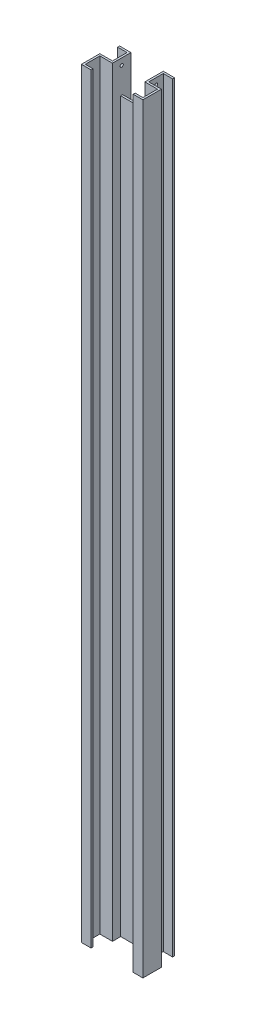
SolidWorks part; units mm, degrees
ref_plane "Front Plane" through (0, 0, 0) normal (0, 0, 1) x (1, 0, 0)
ref_plane "Top Plane" through (0, 0, 0) normal (0, 1, 0) x (1, 0, 0)
ref_plane "Right Plane" through (0, 0, 0) normal (1, 0, 0) x (0, 0, -1)
ref_plane "Plane1" through (0, 0, -76.5) normal (0, 0, -1) x (-1, 0, 0)
sketch "Sketch1" plane through (0, 0, -76.5) normal (0, 0, -1) x (-1, 0, 0)
  line L0 (-95, 0) -> (-50, 0)
  line L1 (-50, 0) -> (-50, 2350)
  line L2 (-50, 2350) -> (-95, 2350)
  line L3 (-95, 2350) -> (-95, 0)
extrude "Boss-Extrude1" add sketch "Sketch1" against normal blind 31.5
sketch "Sketch2" plane through (50, 0, 0) normal (-1, 0, 0) x (0, 0, 1)
  line L0 (-70.5, 0) -> (-76.5, 0)
  line L1 (-76.5, 0) -> (-76.5, 2350)
  line L2 (-76.5, 2350) -> (-70.5, 2350)
  line L3 (-70.5, 2350) -> (-70.5, 0)
extrude "Boss-Extrude2" add sketch "Sketch2" along normal blind 145
sketch "Sketch3" plane through (0, 0, -70.5) normal (0, 0, 1) x (1, 0, 0)
  line L0 (-50, 0) -> (-95, 0)
  line L1 (-95, 0) -> (-95, 2350)
  line L2 (-95, 2350) -> (-50, 2350)
  line L3 (-50, 2350) -> (-50, 0)
extrude "Boss-Extrude3" add sketch "Sketch3" along normal blind 76.5
sketch "Sketch4" plane through (0, 0, -45) normal (0, 0, 1) x (1, 0, 0)
  line L0 (89, 2350) -> (95, 2350)
  line L1 (95, 2350) -> (95, 0)
  line L2 (95, 0) -> (89, 0)
  line L3 (89, 0) -> (89, 2350)
extrude "Boss-Extrude4" add sketch "Sketch4" along normal blind 51
sketch "Sketch5" plane through (89, 0, 0) normal (-1, 0, 0) x (0, 0, 1)
  line L0 (6, 0) -> (0, 0)
  line L1 (0, 0) -> (0, 2350)
  line L2 (0, 2350) -> (6, 2350)
  line L3 (6, 2350) -> (6, 0)
extrude "Boss-Extrude5" add sketch "Sketch5" along normal blind 24
sketch "Sketch6" plane through (0, 0, 6) normal (0, 0, 1) x (1, 0, 0)
  line L0 (-65, 2350) -> (-65, 0)
  line L1 (-65, 0) -> (-50, 0)
  line L2 (-50, 0) -> (-50, 2350)
  line L3 (-50, 2350) -> (-65, 2350)
extrude "Cut-Extrude1" cut sketch "Sketch6" against normal blind 6
sketch "Sketch7" plane through (0, 0, 0) normal (0, 0, 1) x (1, 0, 0)
  line L0 (-89, 0) -> (-50, 0)
  line L1 (-50, 0) -> (-50, 2350)
  line L2 (-50, 2350) -> (-89, 2350)
  line L3 (-89, 2350) -> (-89, 0)
extrude "Cut-Extrude2" cut sketch "Sketch7" against normal blind 45
sketch "Sketch8" plane through (0, 2350, 0) normal (0, 1, 0) x (-1, 0, 0)
  line L0 (50, -76.5) -> (50, -70.5)
  line L1 (50, -70.5) -> (-50, -70.5)
  line L2 (-50, -70.5) -> (-50, -76.5)
  line L3 (-50, -76.5) -> (50, -76.5)
extrude "Cut-Extrude3" cut sketch "Sketch8" against normal blind 100
sketch "Sketch9" plane through (0, 0, -76.5) normal (0, 0, -1) x (-1, 0, 0)
  line L0 (-95, 2350) -> (-50, 2350)
  line L1 (-50, 2350) -> (-50, 0)
  line L2 (-50, 0) -> (-95, 0)
  line L3 (-95, 0) -> (-95, 2350)
extrude "Boss-Extrude6" add sketch "Sketch9" along normal blind 25.5
sketch "Sketch10" plane through (0, 0, 0) normal (0, -1, 0) x (1, 0, 0)
  line L0 (95, -102) -> (95, -51)
  line L1 (95, -51) -> (56, -51)
  line L2 (56, -51) -> (56, -102)
  line L3 (56, -102) -> (95, -102)
extrude "Cut-Extrude4" cut sketch "Sketch10" against normal through all
sketch "Sketch11" plane through (56, 0, 0) normal (1, 0, 0) x (0, 0, -1)
  line L0 (102, 0) -> (96, 0)
  line L1 (96, 0) -> (96, 2350)
  line L2 (96, 2350) -> (102, 2350)
  line L3 (102, 2350) -> (102, 0)
extrude "Boss-Extrude7" add sketch "Sketch11" along normal blind 29
sketch "Sketch12" plane through (0, 0, -76.5) normal (0, 0, -1) x (-1, 0, 0)
  line L0 (95, 0) -> (50, 0)
  line L1 (50, 0) -> (50, 2350)
  line L2 (50, 2350) -> (95, 2350)
  line L3 (95, 2350) -> (95, 0)
extrude "Boss-Extrude8" add sketch "Sketch12" along normal blind 25.5
sketch "Sketch13" plane through (0, 2350, 0) normal (0, 1, 0) x (-1, 0, 0)
  line L0 (95, -51) -> (56, -51)
  line L1 (56, -51) -> (56, -102)
  line L2 (56, -102) -> (95, -102)
  line L3 (95, -102) -> (95, -51)
extrude "Cut-Extrude5" cut sketch "Sketch13" against normal through all
sketch "Sketch14" plane through (-56, 0, 0) normal (-1, 0, 0) x (0, 0, 1)
  line L0 (-96, 0) -> (-102, 0)
  line L1 (-102, 0) -> (-102, 2350)
  line L2 (-102, 2350) -> (-96, 2350)
  line L3 (-96, 2350) -> (-96, 0)
extrude "Boss-Extrude9" add sketch "Sketch14" along normal blind 29
hole_wizard "Ø10.0 (10) Diameter Hole1" positions "Sketch16" profile "Sketch15" hole size "Ø10.0" standard "ANSI Metric"
sketch "Sketch16" plane through (-56, 0, 0) normal (-1, 0, 0) x (0, 0, 1)
  point P0 (-73.5, 2330)
sketch "Sketch15" plane through (-56, 2330, -73.5) normal (0, 1, 0) x (0, 0, 1)
  line L0 (0, 0) -> (0, 6)
  line L1 (0, 6) -> (5, 6)
  line L2 (5, 6) -> (5, 0)
  line L5 (5, 0) -> (0, 0)
  line L11 (0, -6.35) -> (0, 107.95) construction
  dimension "Thru Hole Dia." = 10
  dimension "Thru Hole Depth" = 6
hole_wizard "Ø10.0 (10) Diameter Hole2" positions "Sketch18" profile "Sketch17" hole size "Ø10.0" standard "ANSI Metric"
sketch "Sketch18" plane through (50, 0, 0) normal (-1, 0, 0) x (0, 0, 1)
  point P0 (-73.5, 2330)
sketch "Sketch17" plane through (50, 2330, -73.5) normal (0, 1, 0) x (0, 0, 1)
  line L0 (0, 0) -> (0, 45)
  line L1 (0, 45) -> (5, 45)
  line L2 (5, 45) -> (5, 0)
  line L5 (5, 0) -> (0, 0)
  line L11 (0, -6.35) -> (0, 107.95) construction
  dimension "Thru Hole Dia." = 10
  dimension "Thru Hole Depth" = 45
